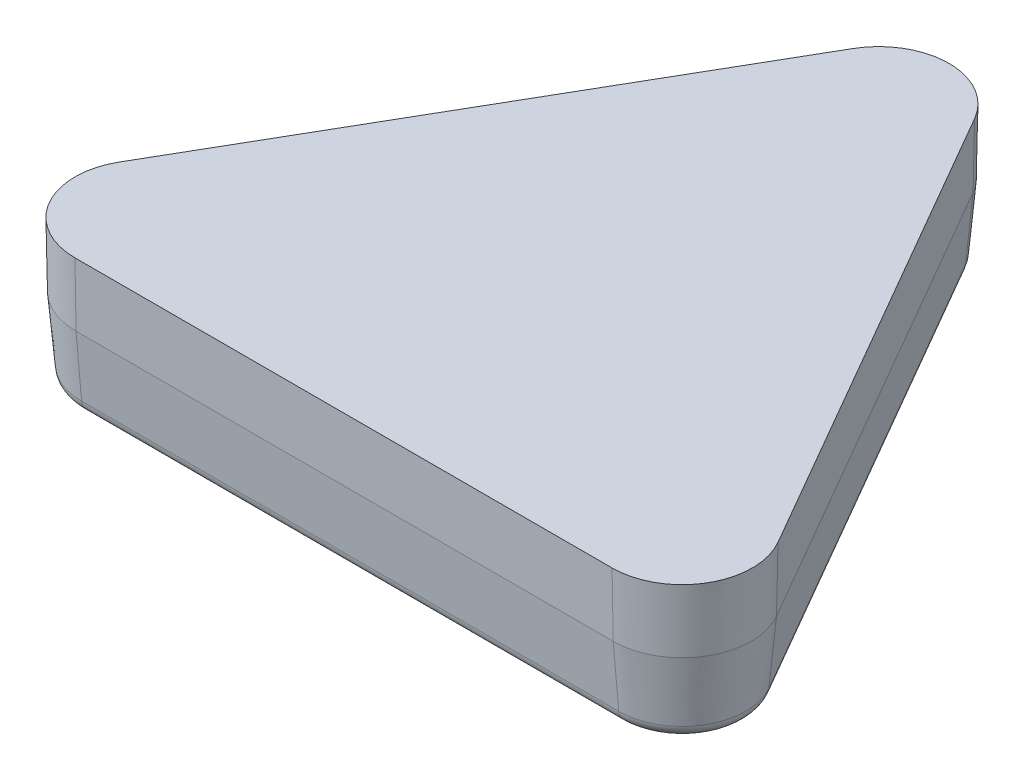
SolidWorks part; units mm, degrees
material "CA"
ref_plane "Front Plane" through (0, 0, 0) normal (0, 0, 1) x (1, 0, 0)
ref_plane "Top Plane" through (0, 0, 0) normal (0, 1, 0) x (1, 0, 0)
ref_plane "Right Plane" through (0, 0, 0) normal (1, 0, 0) x (0, 0, -1)
sketch "Sketch1" plane through (0, 0, 0) normal (0, 1, 0) x (1, 0, 0)
  line L0 (0, 0) -> (0, 14.0377) construction
  line L1 (-2.7496, 15.6252) -> (-14.9067, -5.4314)
  line L2 (-12.157, -10.1939) -> (12.157, -10.1939)
  line L3 (14.9067, -5.4314) -> (2.7496, 15.6252)
  circle A0 centre (0, 0) radius 19.05 construction
  circle A1 centre (0, 0) radius 10.1939 construction
  arc A2 (-14.9067, -5.4314) -> (-12.157, -10.1939) centre (-12.157, -7.0189) ccw
  arc A3 (12.157, -10.1939) -> (14.9067, -5.4314) centre (12.157, -7.0189) ccw
  arc A4 (-2.7496, 15.6252) -> (2.7496, 15.6252) centre (0, 14.0377) cw
  dimension "D3" = 27.4066
  dimension "D1" = 38.1
  dimension "D2" = 3.175
  dimension "D4" = 30.6641
extrude "Boss-Extrude1" add sketch "Sketch1" against normal blind 6.35 draft 1
sketch "Sketch6" plane through (0, 0, 0) normal (0, 0, 1) x (1, 0, 0)
  line L0 (0, 0) -> (0, -2.54) construction
  line L1 (0, -2.54) -> (-6.985, -9.525)
  line L2 (0, -2.54) -> (6.985, -9.525)
  line L3 (-6.985, -9.525) -> (6.985, -9.525)
  line L4 (-12.157, 0) -> (12.157, 0) construction
  dimension "D1" = 2.54
  dimension "D2" = 90
  dimension "D3" = 9.525
extrude "Cut-Extrude3" cut sketch "Sketch6" against normal through all
pattern_circular "CirPattern3" count 24 over 360 about axis through (0, 0, 0) along (0, 1, 0) of "Cut-Extrude3"
sketch "Sketch7" plane through (0, 0, 0) normal (0, 1, 0) x (1, 0, 0)
  line L3 (-12.157, -10.1939) -> (12.157, -10.1939)
  line L4 (-12.157, -10.1939) -> (12.157, -10.1939)
  line L5 (14.9067, -5.4314) -> (2.7496, 15.6252)
  line L6 (14.9067, -5.4314) -> (2.7496, 15.6252)
  line L7 (-2.7496, 15.6252) -> (-14.9067, -5.4314)
  line L8 (-2.7496, 15.6252) -> (-14.9067, -5.4314)
  line L9 (-12.157, -8.0349) -> (12.157, -8.0349)
  line L10 (-12.157, -8.0349) -> (12.157, -8.0349)
  line L11 (13.0369, -6.5109) -> (0.8799, 14.5457)
  line L12 (13.0369, -6.5109) -> (0.8799, 14.5457)
  line L13 (-0.8799, 14.5457) -> (-13.0369, -6.5109)
  line L14 (-0.8799, 14.5457) -> (-13.0369, -6.5109)
  arc A1 (-14.9067, -5.4314) -> (-12.157, -10.1939) centre (-12.157, -7.0189) ccw
  arc A2 (-14.9067, -5.4314) -> (-12.157, -10.1939) centre (-12.157, -7.0189) ccw
  arc A3 (-13.0369, -6.5109) -> (-12.157, -8.0349) centre (-12.157, -7.0189) ccw
  arc A4 (-13.0369, -6.5109) -> (-12.157, -8.0349) centre (-12.157, -7.0189) ccw
  arc A7 (12.157, -10.1939) -> (14.9067, -5.4314) centre (12.157, -7.0189) ccw
  arc A8 (12.157, -10.1939) -> (14.9067, -5.4314) centre (12.157, -7.0189) ccw
  arc A9 (2.7496, 15.6252) -> (-2.7496, 15.6252) centre (0, 14.0377) ccw
  arc A10 (2.7496, 15.6252) -> (-2.7496, 15.6252) centre (0, 14.0377) ccw
  arc A11 (12.157, -8.0349) -> (13.0369, -6.5109) centre (12.157, -7.0189) ccw
  arc A12 (12.157, -8.0349) -> (13.0369, -6.5109) centre (12.157, -7.0189) ccw
  arc A13 (0.8799, 14.5457) -> (-0.8799, 14.5457) centre (0, 14.0377) ccw
  arc A14 (0.8799, 14.5457) -> (-0.8799, 14.5457) centre (0, 14.0377) ccw
  dimension "D1" = 0
  dimension "D2" = 2.159
extrude "Boss-Extrude3" add sketch "Sketch7" against normal blind 6.35 draft 1
sketch "Sketch8" plane through (0, 0, 0) normal (0, 1, 0) x (1, 0, 0)
  line L6 (-12.157, -10.3971) -> (12.157, -10.3971)
  line L7 (15.0826, -5.3298) -> (2.9256, 15.7268)
  line L8 (-2.9256, 15.7268) -> (-15.0826, -5.3298)
  line L9 (-12.157, -10.3971) -> (12.157, -10.3971)
  line L10 (15.0826, -5.3298) -> (2.9256, 15.7268)
  line L11 (-2.9256, 15.7268) -> (-15.0826, -5.3298)
  arc A6 (-15.0826, -5.3298) -> (-12.157, -10.3971) centre (-12.157, -7.0189) ccw
  arc A7 (12.157, -10.3971) -> (15.0826, -5.3298) centre (12.157, -7.0189) ccw
  arc A8 (2.9256, 15.7268) -> (-2.9256, 15.7268) centre (0, 14.0377) ccw
  arc A9 (-15.0826, -5.3298) -> (-12.157, -10.3971) centre (-12.157, -7.0189) ccw
  arc A10 (12.157, -10.3971) -> (15.0826, -5.3298) centre (12.157, -7.0189) ccw
  arc A11 (2.9256, 15.7268) -> (-2.9256, 15.7268) centre (0, 14.0377) ccw
  dimension "D1" = 0.2032
extrude "Cut-Extrude4" cut sketch "Sketch8" against normal through all draft 5 flip side to cut draft outward yes
draft "Draft2" type of draft neutral plane draft angle 5 faces to draft 6 face at (-12.8636, -4.4652, 7.4268) face at (-7.0127, -3.5952, -4.0488) face at (0, -4.4652, -14.8536) face at (7.0127, -3.5952, -4.0488) face at (12.8636, -4.4652, 7.4268) face at (0, -3.5952, 8.0976) neutral plane through (-12.157, 0, 7.0189) neutral plane normal (0, 1, 0) reverse direction yes parameters "D1"=5
fillet "Fillet2" radius 0.635 12 edges at (-14.6015, -6.35, 8.4302) (-8.523, -6.35, -4.9208) (0, -6.35, -16.8604) (8.523, -6.35, -4.9208) (14.6015, -6.35, 8.4302) (13.518, -6.35, 7.8046) (0, -6.35, 8.5904) (-13.518, -6.35, 7.8046) (-7.4395, -6.35, -4.2952) (0, -6.35, -15.6093) (0, -6.35, 9.8415) (7.4395, -6.35, -4.2952)
sketch "Sketch11 - OFFSET .005" plane through (0, 0, 0) normal (0, 1, 0) x (1, 0, 0)
  line L3 (-12.157, -10.3209) -> (12.157, -10.3209)
  line L4 (-12.157, -10.3209) -> (12.157, -10.3209)
  line L5 (15.0166, -5.3679) -> (2.8596, 15.6887)
  line L6 (15.0166, -5.3679) -> (2.8596, 15.6887)
  line L7 (-2.8596, 15.6887) -> (-15.0166, -5.3679)
  line L8 (-2.8596, 15.6887) -> (-15.0166, -5.3679)
  arc A1 (-15.0166, -5.3679) -> (-12.157, -10.3209) centre (-12.157, -7.0189) ccw
  arc A2 (-15.0166, -5.3679) -> (-12.157, -10.3209) centre (-12.157, -7.0189) ccw
  arc A5 (12.157, -10.3209) -> (15.0166, -5.3679) centre (12.157, -7.0189) ccw
  arc A6 (12.157, -10.3209) -> (15.0166, -5.3679) centre (12.157, -7.0189) ccw
  arc A7 (2.8596, 15.6887) -> (-2.8596, 15.6887) centre (0, 14.0377) ccw
  arc A8 (2.8596, 15.6887) -> (-2.8596, 15.6887) centre (0, 14.0377) ccw
  dimension "D1" = 0.127
